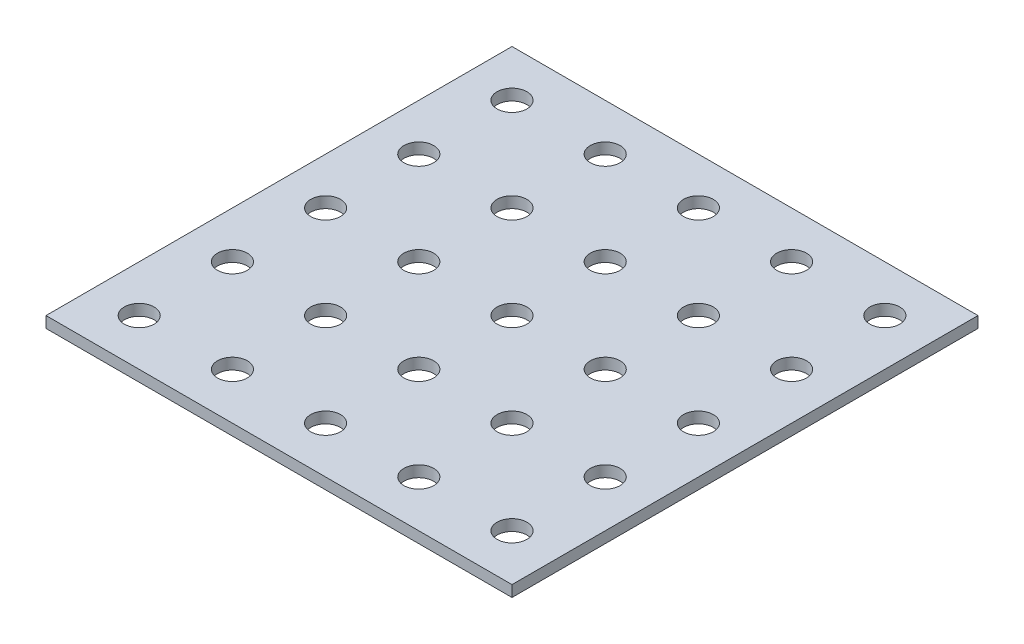
SolidWorks part; units mm, degrees
ref_plane "Спереди" through (0, 0, 0) normal (0, 0, 1) x (1, 0, 0)
ref_plane "Сверху" through (0, 0, 0) normal (0, 1, 0) x (1, 0, 0)
ref_plane "Справа" through (0, 0, 0) normal (1, 0, 0) x (0, 0, -1)
other "Configuration Table"
sketch "Эскиз1" plane through (0, 0, 0) normal (0, 1, 0) x (1, 0, 0)
  line L1 (125, 125) -> (-125, 125)
  line L2 (125, 125) -> (125, -125)
  line L3 (125, -125) -> (-125, -125)
  line L4 (-125, 125) -> (-125, -125)
  line L5 (125, 125) -> (-125, -125) construction
  line L6 (125, -125) -> (-125, 125) construction
  point P0 (0, 0)
  dimension "D1" = 250
  dimension "D2" = 250
extrude "Бобышка-Вытянуть1" add sketch "Эскиз1" along normal blind 6
sketch "Эскиз2" plane through (0, 6, 0) normal (0, 1, 0) x (1, 0, 0)
  line L0 (-125, 125) -> (-125, -125) construction
  line L1 (-125, -125) -> (125, -125) construction
  line L2 (-100, -100) -> (-50, -100) construction
  line L3 (-100, -100) -> (-100, -50) construction
  circle A0 centre (-100, -100) radius 8
  circle A1 centre (-50, -100) radius 8
  circle A2 centre (0, -100) radius 8
  circle A3 centre (50, -100) radius 8
  circle A4 centre (100, -100) radius 8
  circle A5 centre (-50, -50) radius 8
  circle A6 centre (0, -50) radius 8
  circle A7 centre (50, -50) radius 8
  circle A8 centre (100, -50) radius 8
  circle A9 centre (-50, 0) radius 8
  circle A10 centre (0, 0) radius 8
  circle A11 centre (50, 0) radius 8
  circle A12 centre (100, 0) radius 8
  circle A13 centre (-50, 50) radius 8
  circle A14 centre (0, 50) radius 8
  circle A15 centre (50, 50) radius 8
  circle A16 centre (100, 50) radius 8
  circle A17 centre (-50, 100) radius 8
  circle A18 centre (0, 100) radius 8
  circle A19 centre (50, 100) radius 8
  circle A20 centre (100, 100) radius 8
  circle A21 centre (-100, -50) radius 8
  circle A22 centre (-100, 0) radius 8
  circle A23 centre (-100, 50) radius 8
  circle A24 centre (-100, 100) radius 8
  dimension "D4" = 16
  dimension "D1" = 25
  dimension "D2" = 25
  dimension "D5" = 50
  dimension "D6" = 50
  dimension "D7" = 5
  dimension "D3" = 5
extrude "Вырез-Вытянуть1" cut sketch "Эскиз2" against normal blind 6
equation "\"D2@Эскиз2\"=\"D1@Эскиз2\""
